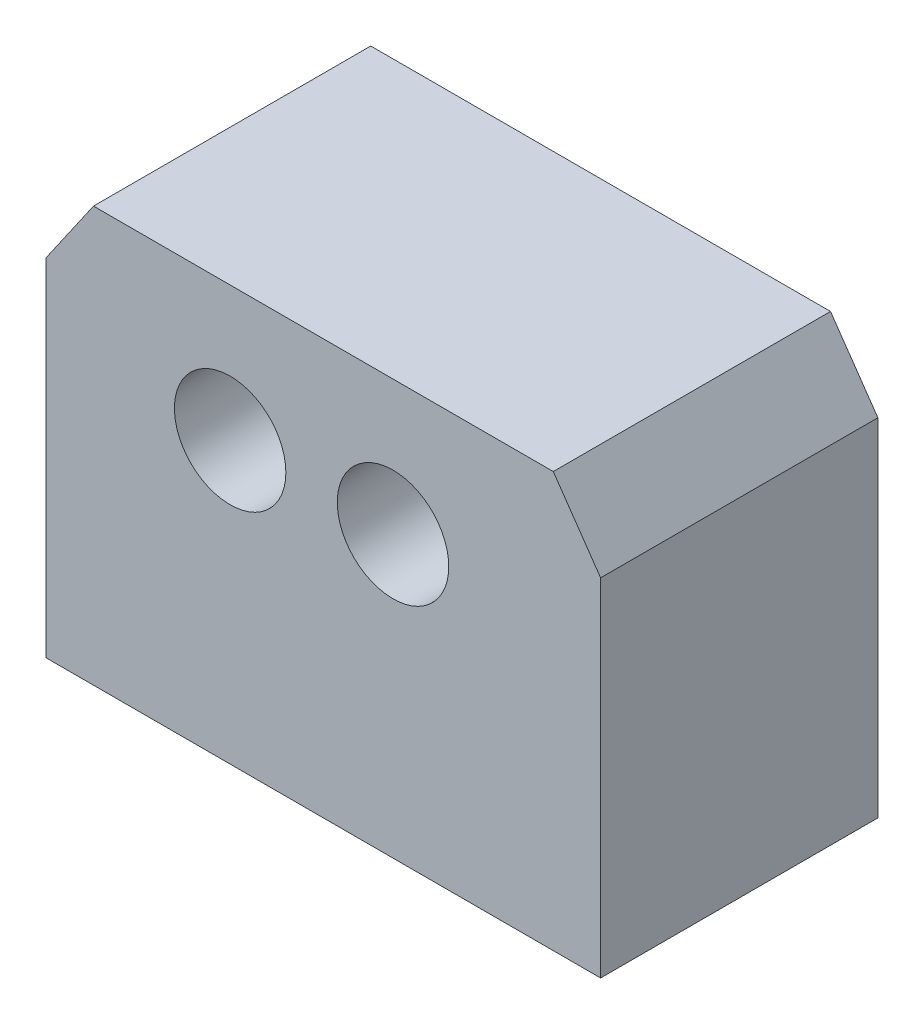
SolidWorks part; units mm, degrees
material "ABS"
ref_plane "Plano frontal" through (0, 0, 0) normal (0, 0, 1) x (1, 0, 0)
ref_plane "Plano superior" through (0, 0, 0) normal (0, 1, 0) x (1, 0, 0)
ref_plane "Plano direito" through (0, 0, 0) normal (1, 0, 0) x (0, 0, -1)
sketch "Esboço1" plane through (0, 0, 0) normal (0, 0, 1) x (1, 0, 0)
  line L1 (19.9063, -10.2224) -> (-20.0937, -10.2224)
  line L2 (19.9063, -10.2224) -> (19.9063, 4.7776)
  line L4 (-20.0937, -10.2224) -> (-20.0937, 4.7776)
  line L5 (19.9063, -10.2224) -> (-25.5819, 13.137) construction
  line L6 (19.0863, 9.7099) -> (-20.0937, -10.2224) construction
  line L8 (-20.0937, 0) -> (-5.9687, 0) construction
  line L9 (-5.9687, 0) -> (-6.8199, 0) construction
  line L10 (-6.8199, 0) -> (4.9301, 0) construction
  line L11 (4.9301, 0) -> (5.7813, 0) construction
  line L12 (5.7813, 0) -> (19.9063, 0) construction
  line L13 (-20.0937, 4.7776) -> (-16.6772, 9.7099)
  line L14 (-16.6772, 9.7099) -> (16.4898, 9.7099)
  line L15 (16.4898, 9.7099) -> (19.9063, 4.7776)
  circle A0 centre (-6.8199, 0) radius 4.0203
  circle A1 centre (4.9301, 0) radius 4.0203
  point P0 (0, 0)
  dimension "D1" = 40
  dimension "D6" = 15
  dimension "D2" = 15
  dimension "D5" = 11.75
extrude "Ressalto-extrusão1" add sketch "Esboço1" along normal blind 20
sketch "Esboço2" plane through (0, -10.2224, 0) normal (0, -1, 0) x (1, 0, 0)
  line L1 (-20.0937, 20) -> (19.9063, 20)
  line L2 (-20.0937, 20) -> (-20.0937, 0)
  line L3 (-20.0937, 0) -> (19.9063, 0)
  line L4 (19.9063, 20) -> (19.9063, 0)
extrude "Ressalto-extrusão2" add sketch "Esboço2" along normal blind 10
